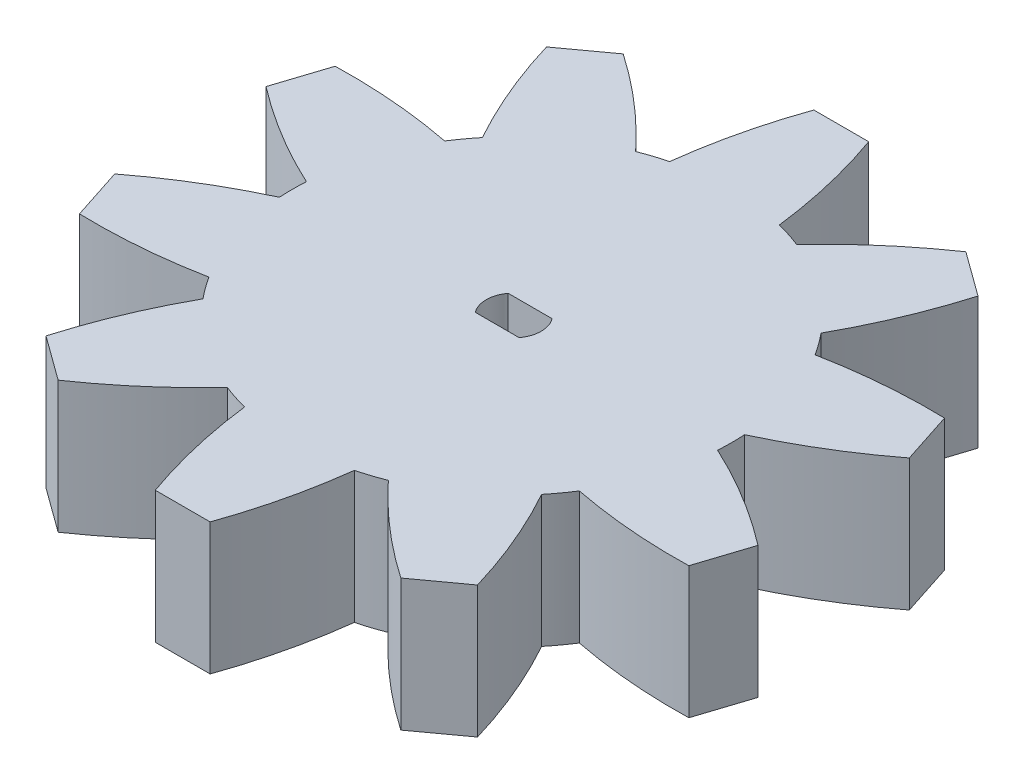
SolidWorks part; units mm, degrees
ref_plane "Front Plane" through (0, 0, 0) normal (0, 0, 1) x (1, 0, 0)
ref_plane "Top Plane" through (0, 0, 0) normal (0, 1, 0) x (1, 0, 0)
ref_plane "Right Plane" through (0, 0, 0) normal (1, 0, 0) x (0, 0, -1)
sketch "Sketch1" plane through (0, 0, 0) normal (0, 1, 0) x (1, 0, 0)
  circle A0 centre (0, 0) radius 20
  dimension "D1" = 40
extrude "Boss-Extrude1" add sketch "Sketch1" along normal blind 12
sketch "Sketch2" plane through (0, 12, 0) normal (0, 1, 0) x (1, 0, 0)
  line L2 (-1.9604, 1.6142) -> (2.0396, 1.6142)
  line L3 (-1.9604, -1.3858) -> (2.0396, -1.3858)
  arc A0 (-1.9604, 1.6142) -> (-1.9604, -1.3858) centre (0.0396, 0.1142) ccw
  arc A1 (2.0396, 1.6142) -> (2.0396, -1.3858) centre (0.0396, 0.1142) cw
extrude "Cut-Extrude1" cut sketch "Sketch2" against normal blind 6
sketch "Sketch3" plane through (0, 12, 0) normal (0, 1, 0) x (1, 0, 0)
  point P9 (5.3913, 19.2596)
sketch "Sketch4" plane through (0, 12, 0) normal (0, 1, 0) x (1, 0, 0)
  line L1 (-2.5, 30) -> (2.5, 30)
  circle A0 centre (0, 0) radius 20 construction
  arc A3 (-5, 19.3649) -> (5, 19.3649) centre (0, 0) cw
  arc A4 (-2.5, 30) -> (-5, 19.3649) centre (44.6319, 13.3093) ccw
  arc A5 (2.5, 30) -> (5, 19.3649) centre (-44.6319, 13.3093) cw
  point P0 (0, 20)
  point P1 (5, 19.3649)
  point P4 (-5, 19.3649)
  dimension "D1" = 10
  dimension "D6" = 50
  dimension "D2" = 5
  dimension "D4" = 5
extrude "Boss-Extrude2" add sketch "Sketch4" against normal blind 12
pattern_circular "CirPattern2" count 10 over 360 about axis through (0, 0, 0) along (0, 1, 0) of "Boss-Extrude2"
